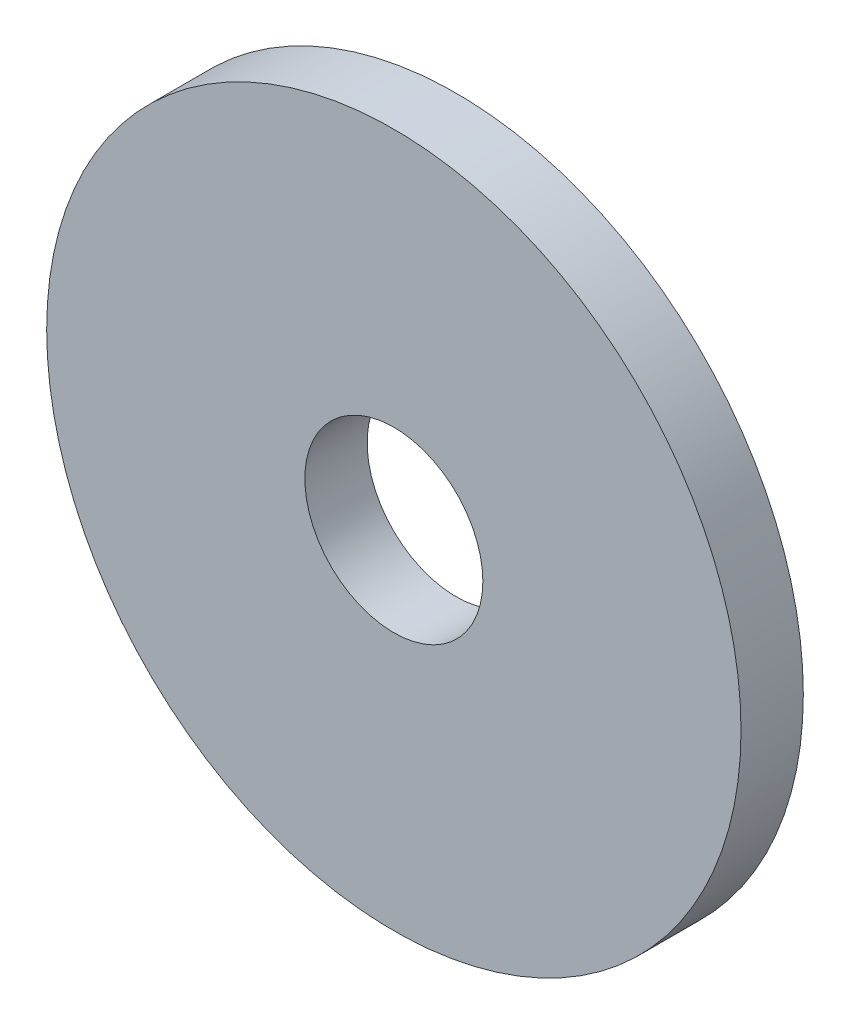
SolidWorks part; units mm, degrees
material "PE Low/Medium Density"
ref_plane "Front Plane" through (0, 0, 0) normal (0, 0, 1) x (1, 0, 0)
ref_plane "Top Plane" through (0, 0, 0) normal (0, 1, 0) x (1, 0, 0)
ref_plane "Right Plane" through (0, 0, 0) normal (1, 0, 0) x (0, 0, -1)
sketch "Sketch1" plane through (0, 0, 0) normal (0, 0, 1) x (1, 0, 0)
  circle A0 centre (0, 0) radius 3.4671
  circle A1 centre (0, 0) radius 0.889
  dimension "D1" = 6.9342
  dimension "D2" = 1.778
extrude "Plate" add sketch "Sketch1" along normal blind 0.6223
